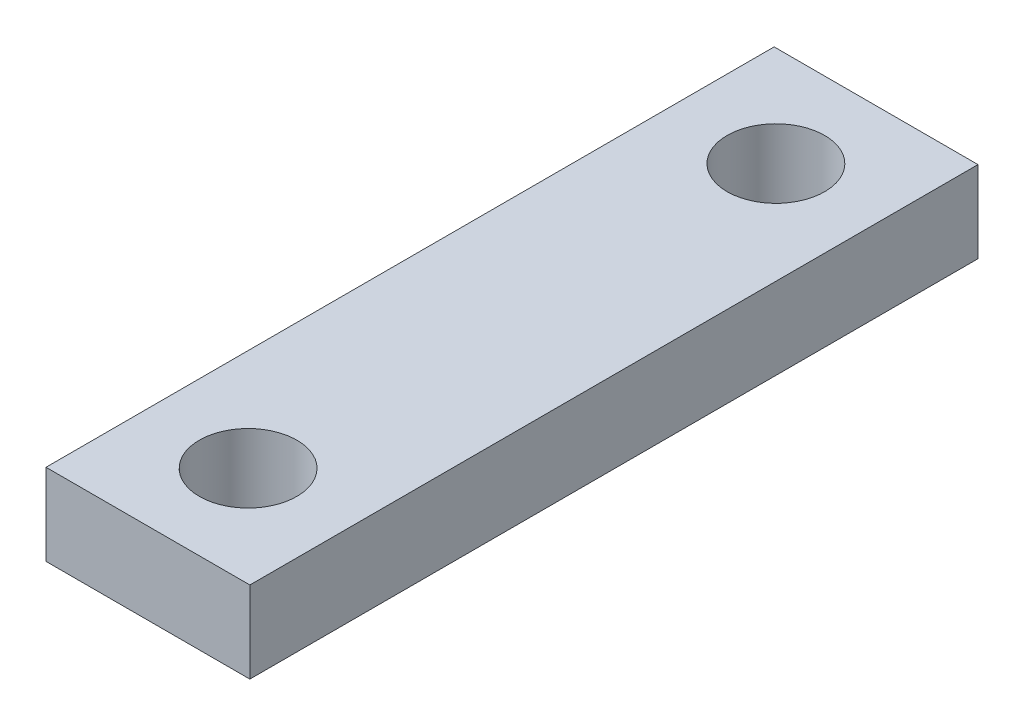
SolidWorks part; units mm, degrees
ref_plane "Front Plane" through (0, 0, 0) normal (0, 0, 1) x (1, 0, 0)
ref_plane "Top Plane" through (0, 0, 0) normal (0, 1, 0) x (1, 0, 0)
ref_plane "Right Plane" through (0, 0, 0) normal (1, 0, 0) x (0, 0, -1)
sketch "Sketch1" plane through (0, 0, 0) normal (0, 0, 1) x (1, 0, 0)
  line L1 (0, 0) -> (7.9375, 0)
  line L2 (0, 0) -> (0, 3.175)
  line L3 (0, 3.175) -> (7.9375, 3.175)
  line L4 (7.9375, 0) -> (7.9375, 3.175)
  dimension "D1" = 7.9375
  dimension "D2" = 3.175
extrude "Boss-Extrude2" add sketch "Sketch1" along normal blind 28.35
sketch "Sketch3" plane through (0, 3.175, 0) normal (0, 1, 0) x (1, 0, 0)
  line L0 (3.9688, 0) -> (3.9688, -28.35) construction
  line L1 (7.9375, 0) -> (0, 0) construction
  line L2 (7.9375, -28.35) -> (0, -28.35) construction
  line L3 (0, -14.175) -> (7.9375, -14.175) construction
  line L4 (0, -28.35) -> (0, 0) construction
  line L5 (7.9375, -28.35) -> (7.9375, 0) construction
  circle A0 centre (3.9688, -3.9) radius 1.8987
  circle A1 centre (3.9688, -24.45) radius 1.8987
  dimension "D1" = 3.7973
  dimension "D2" = 3.7973
  dimension "D3" = 10.275
  dimension "D4" = 10.275
extrude "Cut-Extrude1" cut sketch "Sketch3" against normal through all
